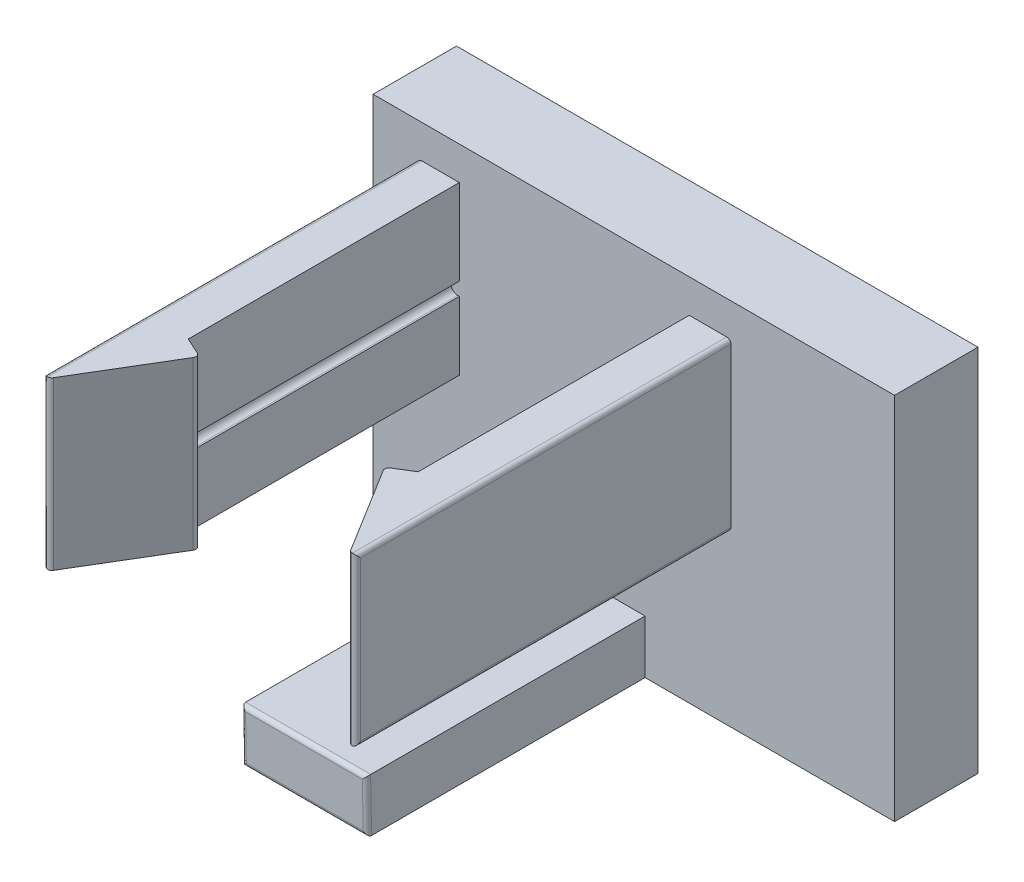
SolidWorks part; units mm, degrees
ref_plane "Front Plane" through (0, 0, 0) normal (0, 0, 1) x (1, 0, 0)
ref_plane "Top Plane" through (0, 0, 0) normal (0, 1, 0) x (1, 0, 0)
ref_plane "Right Plane" through (0, 0, 0) normal (1, 0, 0) x (0, 0, -1)
sketch "Sketch1" plane through (0, 0, 0) normal (0, 0, 1) x (1, 0, 0)
  line L0 (15.875, -38.1) -> (15.875, 38.1) construction
  line L1 (0, -24.8983) -> (15.875, -24.8983)
  line L2 (0, -24.8983) -> (0, -13.6585)
  line L3 (0, -13.6585) -> (15.875, -13.6585)
  line L4 (15.875, -24.8983) -> (15.875, -13.6585)
  dimension "D1" = 11.2398
  dimension "D2" = 15.875
extrude "Boss-Extrude1" add sketch "Sketch1" along normal blind 2.54 contours L2 L3 L4 L1
sketch "Sketch2" plane through (0, 0, 2.54) normal (0, 0, 1) x (1, 0, 0)
  line L0 (2.625, -17.674) -> (2.625, -19.754)
  line L1 (9.625, -14.674) -> (10.895, -14.674)
  line L2 (9.625, -14.674) -> (9.625, -19.754)
  line L3 (9.625, -19.754) -> (10.895, -19.754)
  line L4 (10.895, -14.674) -> (10.895, -19.754)
  line L5 (2.625, -19.754) -> (1.355, -19.754)
  line L6 (1.355, -19.754) -> (1.355, -14.674)
  line L7 (1.355, -14.674) -> (2.625, -14.674)
  line L8 (2.625, -14.674) -> (2.625, -17.274)
  line L9 (0, -24.8983) -> (15.875, -24.8983) construction
  line L10 (4.47, -23.274) -> (8.28, -23.274)
  line L11 (4.47, -23.274) -> (4.47, -24.8983)
  line L12 (4.47, -24.8983) -> (8.28, -24.8983)
  line L13 (8.28, -23.274) -> (8.28, -24.8983)
  line L16 (2.375, -17.274) -> (2.375, -17.474)
  line L17 (2.625, -17.274) -> (2.375, -17.274)
  line L18 (2.625, -14.174) -> (2.625, -17.274)
  line L19 (3.625, -14.074) -> (2.725, -14.074)
  line L20 (3.625, -14.674) -> (3.625, -14.074)
  line L21 (6.025, -14.674) -> (3.625, -14.674)
  line L22 (6.025, -16.574) -> (6.025, -14.674)
  line L23 (7.225, -16.574) -> (6.025, -16.574)
  line L24 (7.225, -14.674) -> (7.225, -16.574)
  line L25 (8.925, -14.674) -> (7.225, -14.674)
  line L26 (8.925, -14.074) -> (8.925, -14.674)
  line L27 (9.625, -14.074) -> (8.925, -14.074)
  line L28 (9.625, -23.274) -> (9.625, -14.074)
  line L29 (3.125, -23.274) -> (9.625, -23.274)
  line L30 (2.625, -17.674) -> (2.625, -22.774)
  line L31 (2.575, -17.674) -> (2.625, -17.674)
  line L32 (2.375, -17.274) -> (2.375, -17.474)
  line L33 (2.625, -17.274) -> (2.375, -17.274)
  line L34 (2.625, -14.174) -> (2.625, -17.274) construction
  line L35 (3.625, -14.074) -> (2.725, -14.074) construction
  line L36 (3.625, -14.674) -> (3.625, -14.074) construction
  line L37 (6.025, -14.674) -> (3.625, -14.674) construction
  line L38 (6.025, -16.574) -> (6.025, -14.674) construction
  line L39 (7.225, -16.574) -> (6.025, -16.574) construction
  line L40 (7.225, -14.674) -> (7.225, -16.574) construction
  line L41 (8.925, -14.674) -> (7.225, -14.674) construction
  line L42 (8.925, -14.074) -> (8.925, -14.674) construction
  line L43 (9.625, -14.074) -> (8.925, -14.074) construction
  line L44 (9.625, -23.274) -> (9.625, -14.074) construction
  line L45 (3.125, -23.274) -> (9.625, -23.274) construction
  line L46 (2.625, -17.674) -> (2.625, -22.774) construction
  line L47 (2.575, -17.674) -> (2.625, -17.674)
  arc A3 (2.375, -17.474) -> (2.575, -17.674) centre (2.575, -17.474) ccw
  arc A4 (2.725, -14.074) -> (2.625, -14.174) centre (2.725, -14.174) ccw
  arc A5 (2.625, -22.774) -> (3.125, -23.274) centre (3.125, -22.774) ccw
  arc A6 (2.375, -17.474) -> (2.575, -17.674) centre (2.575, -17.474) ccw
  arc A7 (2.725, -14.074) -> (2.625, -14.174) centre (2.725, -14.174) ccw construction
  arc A8 (2.625, -22.774) -> (3.125, -23.274) centre (3.125, -22.774) ccw construction
  point P34 (6.375, -23.274)
  point P36 (6.375, -23.274)
  dimension "D2" = 5.08
  dimension "D3" = 3.81
  dimension "D4" = 1.27
  dimension "D1" = 0
extrude "Boss-Extrude2" add sketch "Sketch2" along normal offset from surface (8.6312 mm away) 0.381
ref_plane "Plane1" through (2.475, -11.2099, 7.5001) normal (1, 0, 0) x (0, 0, -1)
sketch "Sketch4" plane through (0, -14.674, 0) normal (0, -1, 0) x (1, 0, 0)
  line L0 (10.895, 11.0825) -> (9.625, 11.0825)
  line L1 (8.9926, 11.1817) -> (10.895, 14.2575)
  line L2 (10.895, 14.2575) -> (10.895, 11.0825)
  line L3 (1.355, 11.0825) -> (2.625, 11.0825)
  line L4 (3.26, 11.0825) -> (1.355, 14.2575)
  line L5 (1.355, 14.2575) -> (1.355, 11.0825)
  line L6 (8.9926, 11.1817) -> (9.625, 10.7906)
  line L8 (9.625, 10.7906) -> (9.625, 11.0825)
  line L9 (3.26, 11.0825) -> (2.625, 10.7906)
  line L10 (2.625, 11.0825) -> (2.625, 2.54) construction
  line L11 (2.625, 10.7906) -> (2.625, 11.0825)
  line L12 (9.625, 10.8006) -> (9.625, 10.64) construction
  line L13 (9.625, 11.1712) -> (9.625, 2.54) construction
  line L14 (2.625, 11.1712) -> (2.625, 2.54) construction
  point P9 (0, 0)
  point P19 (0, 0)
  point P21 (9.625, 10.7906)
  point P24 (2.625, 10.7906)
  dimension "D1" = 1.905
  dimension "D2" = 3.175
extrude "Boss-Extrude3" add sketch "Sketch4" along normal up to surface (5.08 mm away) up to face at (1.99, -19.754, 6.8112)
fillet "Fillet1" radius 0.127 12 edges at (1.355, -14.674, 8.3987) (1.355, -19.754, 8.3987) (10.895, -14.674, 8.3987) (10.895, -19.754, 8.3987) (4.47, -24.0861, 11.0069) (8.28, -24.0861, 11.0069) (6.375, -23.274, 11.0211) (6.375, -24.8983, 10.9927) (10.895, -17.214, 14.2575) (1.355, -17.214, 14.2575) (8.9926, -17.214, 11.1817) (3.26, -17.214, 11.0825)
